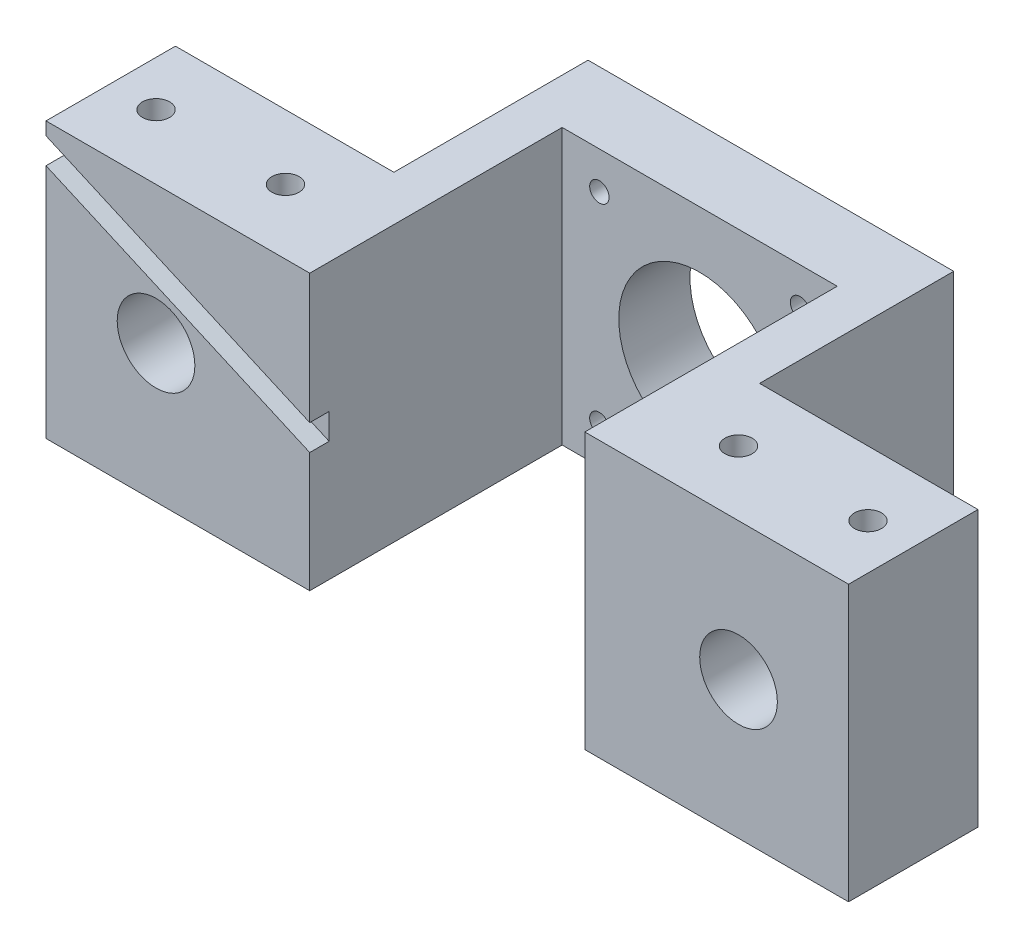
SolidWorks part; units mm, degrees
material "6061 Alloy"
ref_plane "Front Plane" through (0, 0, 0) normal (0, 0, 1) x (1, 0, 0)
ref_plane "Top Plane" through (0, 0, 0) normal (0, 1, 0) x (1, 0, 0)
ref_plane "Right Plane" through (0, 0, 0) normal (1, 0, 0) x (0, 0, -1)
sketch "Sketch2" plane through (0, 0, 0) normal (0, 0, 1) x (1, 0, 0)
  line L0 (-22.7624, 21.25) -> (148.1532, 21.25) construction
  line L1 (0, 0) -> (124, 0)
  line L2 (0, 0) -> (0, 42.5)
  line L3 (0, 42.5) -> (124, 42.5)
  line L4 (124, 0) -> (124, 42.5)
  line L6 (62, 84.8426) -> (62, -23.7147) construction
  line L8 (17, 76.7387) -> (17, -25.306) construction
  line L10 (107, -25.0686) -> (107, 87.5299) construction
  circle A0 centre (62, 21.25) radius 12.5
  circle A1 centre (107, 21.25) radius 6
  circle A2 centre (17, 21.25) radius 6
  circle A3 centre (46.5, 36.75) radius 1.5
  circle A4 centre (77.5, 36.75) radius 1.5
  circle A5 centre (77.5, 5.75) radius 1.5
  circle A6 centre (46.5, 5.75) radius 1.5
  dimension "D3" = 25
  dimension "D4" = 3
  dimension "D5" = 31
  dimension "D7" = 12
  dimension "D1" = 124
  dimension "D2" = 42.5
  dimension "D6" = 31
  dimension "D8" = 45
  dimension "D9" = 45
extrude "Boss-Extrude1" add sketch "Sketch2" along normal blind 50
sketch "Sketch3" plane through (0, 0, 50) normal (0, 0, 1) x (1, 0, 0)
  line L0 (124, 42.5) -> (0, 42.5) construction
  line L1 (40.75, 42.5) -> (83.25, 42.5)
  line L2 (40.75, 42.5) -> (40.75, 0)
  line L3 (40.75, 0) -> (83.25, 0)
  line L4 (83.25, 42.5) -> (83.25, 0)
  line L5 (0, 0) -> (124, 0) construction
  line L6 (62, 59.6498) -> (62, -52.3996) construction
  line L7 (0, 42.5) -> (0, 0) construction
  line L8 (124, 0) -> (124, 42.5) construction
  dimension "D1" = 42.5
extrude "Cut-Extrude1" cut sketch "Sketch3" against normal blind 39
sketch "Sketch4" plane through (0, 0, 0) normal (0, 0, -1) x (-1, 0, 0)
  line L0 (-124, 42.5) -> (0, 42.5) construction
  line L1 (-124, 0) -> (-90.25, 0)
  line L2 (-124, 0) -> (-124, 42.5)
  line L3 (-124, 42.5) -> (-90.25, 42.5)
  line L4 (-90.25, 0) -> (-90.25, 42.5)
  line L6 (0, 0) -> (-33.75, 0)
  line L7 (0, 0) -> (0, 42.5)
  line L8 (0, 42.5) -> (-33.75, 42.5)
  line L9 (-33.75, 0) -> (-33.75, 42.5)
  dimension "D1" = 7
  dimension "D2" = 7
extrude "Cut-Extrude2" cut sketch "Sketch4" against normal offset from surface (30 mm away) 20 up to face at (23, 21.25, 50)
sketch "Sketch5" plane through (0, 0, 0) normal (0, -1, 0) x (1, 0, 0)
  line L0 (-15.7219, 40) -> (149.3318, 40) construction
  line L1 (0, 50) -> (40.75, 50) construction
  line L2 (0, 30) -> (33.75, 30) construction
  line L3 (0, 50) -> (0, 30) construction
  line L5 (124, 50) -> (124, 30) construction
  circle A0 centre (7, 40) radius 2.1
  circle A1 centre (27, 40) radius 2.1
  circle A2 centre (97, 40) radius 2.1
  circle A3 centre (117, 40) radius 2.1
  circle A4 centre (17, 40) radius 2.1
  circle A5 centre (107, 40) radius 2.1
  dimension "D1" = 4.2
  dimension "D2" = 7
  dimension "D3" = 27
  dimension "D4" = 7
  dimension "D5" = 27
  dimension "D6" = 17
  dimension "D7" = 17
extrude "Cut-Extrude3" cut sketch "Sketch5" against normal up to next
sketch "Sketch7" plane through (0, 0, 50) normal (0, 0, 1) x (1, 0, 0)
  line L0 (0, 40.5) -> (40.75, 22.5)
  line L1 (40.75, 42.5) -> (40.75, 0) construction
  line L2 (40.75, 22.5) -> (40.75, 18.5)
  line L3 (40.75, 18.5) -> (0, 36.5)
  line L4 (0, 42.5) -> (0, 0) construction
  line L5 (0, 36.5) -> (0, 40.5)
  line L6 (40.75, 42.5) -> (0, 42.5) construction
  dimension "D1" = 4
  dimension "D2" = 20
  dimension "D3" = 2
extrude "Cut-Extrude4" cut sketch "Sketch7" against normal blind 3
